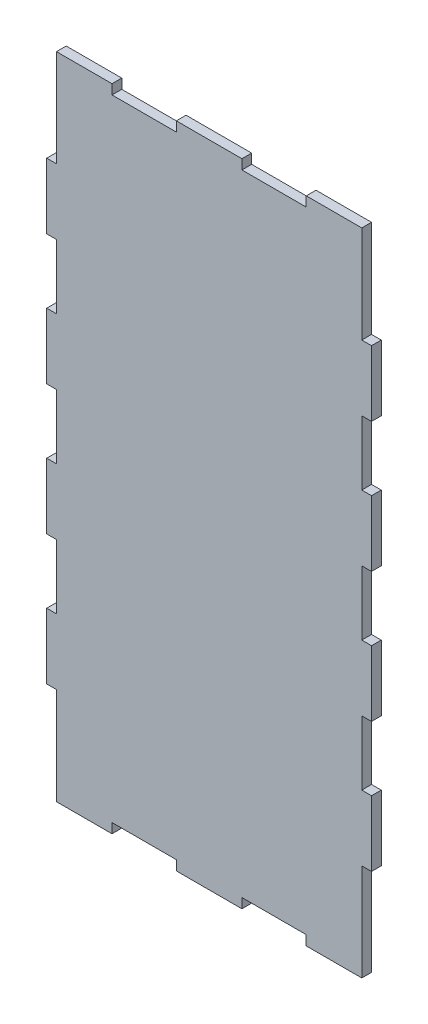
SolidWorks part; units mm, degrees
ref_plane "Front Plane" through (0, 0, 0) normal (0, 0, 1) x (1, 0, 0)
ref_plane "Top Plane" through (0, 0, 0) normal (0, 1, 0) x (1, 0, 0)
ref_plane "Right Plane" through (0, 0, 0) normal (1, 0, 0) x (0, 0, -1)
sketch "Sketch1" plane through (0, 0, 0) normal (0, 0, 1) x (1, 0, 0)
  line L0 (100, 109.9) -> (100, 90.1)
  line L1 (0, 0) -> (100, 0)
  line L2 (0, 0) -> (0, 200)
  line L3 (0, 200) -> (100, 200)
  line L4 (100, 0) -> (100, 200)
  line L5 (97, 200) -> (100, 200)
  line L6 (97, 200) -> (97, 170.1)
  line L7 (97, 170.1) -> (100, 170.1)
  line L8 (100, 200) -> (100, 170.1)
  line L9 (100, 149.9) -> (97, 149.9)
  line L10 (100, 149.9) -> (100, 130.1)
  line L11 (100, 130.1) -> (97, 130.1)
  line L12 (97, 149.9) -> (97, 130.1)
  line L13 (100, 109.9) -> (97, 109.9)
  line L14 (97, 109.9) -> (97, 90.1)
  line L15 (100, 90.1) -> (97, 90.1)
  line L16 (100, 69.9) -> (100, 50.1)
  line L17 (100, 69.9) -> (97, 69.9)
  line L18 (97, 69.9) -> (97, 50.1)
  line L19 (100, 50.1) -> (97, 50.1)
  line L20 (-900, 100) -> (49100, 100) construction
  line L21 (50, -800) -> (50, 49200) construction
  line L22 (97, 29.9) -> (100, 29.9)
  line L23 (100, 0) -> (100, 29.9)
  line L24 (97, 0) -> (100, 0)
  line L25 (97, 0) -> (97, 29.9)
  line L26 (60.1, 200) -> (60.1, 197)
  line L27 (20.1, 200) -> (39.9, 200)
  line L28 (20.1, 200) -> (20.1, 197)
  line L29 (20.1, 197) -> (39.9, 197)
  line L30 (39.9, 200) -> (39.9, 197)
  line L31 (60.1, 200) -> (79.9, 200)
  line L32 (79.9, 200) -> (79.9, 197)
  line L33 (60.1, 197) -> (79.9, 197)
  line L34 (60.1, 0) -> (79.9, 0)
  line L35 (79.9, 0) -> (79.9, 3)
  line L36 (60.1, 3) -> (79.9, 3)
  line L37 (60.1, 0) -> (60.1, 3)
  line L38 (20.1, 3) -> (39.9, 3)
  line L39 (39.9, 0) -> (39.9, 3)
  line L40 (20.1, 0) -> (39.9, 0)
  line L41 (20.1, 0) -> (20.1, 3)
  line L42 (0, 109.9) -> (3, 109.9)
  line L43 (3, 109.9) -> (3, 90.1)
  line L44 (0, 90.1) -> (3, 90.1)
  line L45 (0, 109.9) -> (0, 90.1)
  line L46 (0, 69.9) -> (3, 69.9)
  line L47 (3, 69.9) -> (3, 50.1)
  line L48 (0, 50.1) -> (3, 50.1)
  line L49 (0, 69.9) -> (0, 50.1)
  line L50 (0, 0) -> (0, 29.9)
  line L51 (3, 29.9) -> (0, 29.9)
  line L52 (3, 0) -> (3, 29.9)
  line L53 (3, 0) -> (0, 0)
  line L54 (0, 130.1) -> (3, 130.1)
  line L55 (3, 149.9) -> (3, 130.1)
  line L56 (0, 149.9) -> (3, 149.9)
  line L57 (0, 149.9) -> (0, 130.1)
  line L58 (3, 170.1) -> (0, 170.1)
  line L59 (0, 200) -> (0, 170.1)
  line L60 (3, 200) -> (0, 200)
  line L61 (3, 200) -> (3, 170.1)
  point P23 (100, 100)
  point P26 (50, 200)
  point P34 (79.9, 198.5)
  dimension "D1" = 200
  dimension "D2" = 100
  dimension "D3" = 3
  dimension "D4" = 29.9
  dimension "D5" = 3
  dimension "D6" = 19.8
  dimension "D7" = 20.2
  dimension "D9" = 19.8
  dimension "D10" = 3
  dimension "D11" = 20.1
  dimension "D13" = 20.2
  dimension "D8" = 3
  dimension "D12" = 2
extrude "Boss-Extrude1" add sketch "Sketch1" along normal blind 3 contours L3 L61 L58 L2 L56 L55 L54 L42 L43 L44 L46 L47 L48 L51 L52 L1 L41 L38 L39 L37 L36 L35 L25 L22 L4 L19 L18 L17 L15 L14 L13 L11 L12 L9 L7 L6 L32 L33 L26 L30 L29
